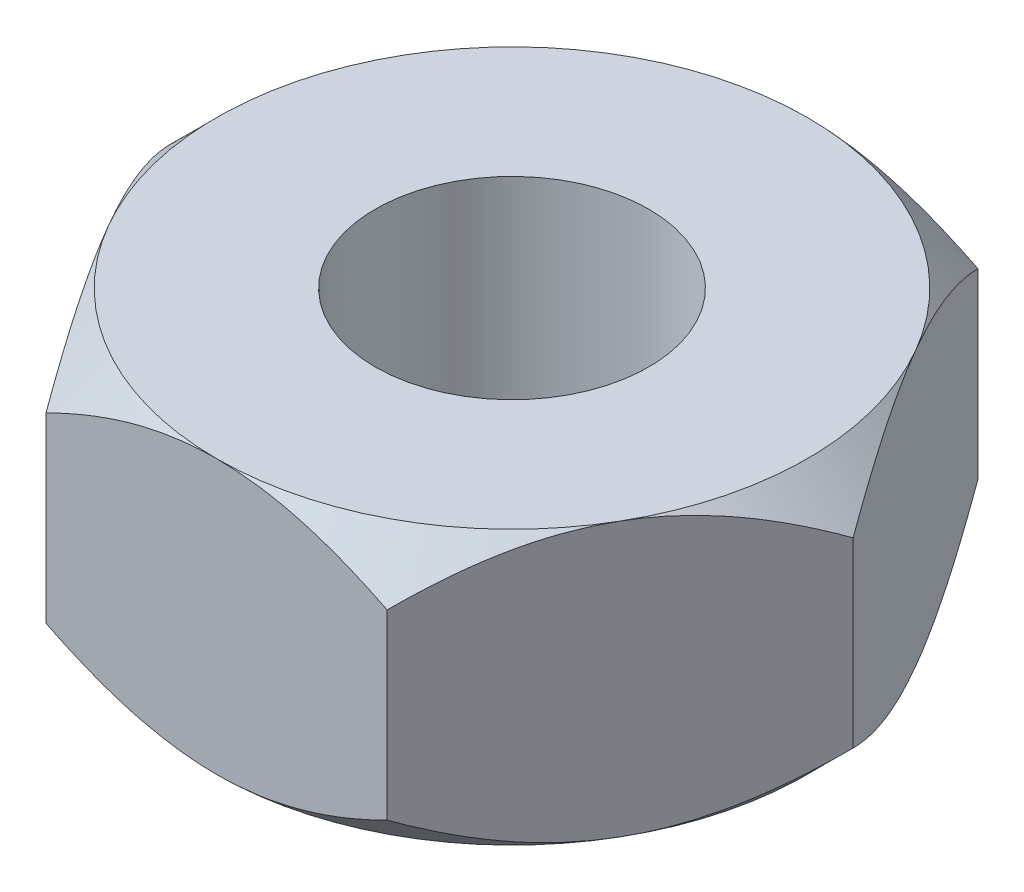
SolidWorks part; units mm, degrees
material "Nylon 6/10"
ref_plane "Front Plane" through (0, 0, 0) normal (0, 0, 1) x (1, 0, 0)
ref_plane "Top Plane" through (0, 0, 0) normal (0, 1, 0) x (1, 0, 0)
ref_plane "Right Plane" through (0, 0, 0) normal (1, 0, 0) x (0, 0, -1)
sketch "Sketch2" plane through (0, 0, 0) normal (0, 1, 0) x (1, 0, 0)
  line L1 (3.1177, 0) -> (1.5588, 2.7)
  line L2 (1.5588, 2.7) -> (-1.5588, 2.7)
  line L3 (-1.5588, 2.7) -> (-3.1177, 0)
  line L4 (-3.1177, 0) -> (-1.5588, -2.7)
  line L5 (-1.5588, -2.7) -> (1.5588, -2.7)
  line L6 (1.5588, -2.7) -> (3.1177, 0)
  circle A0 centre (0, 0) radius 2.7 construction
extrude "Boss-Extrude1" add sketch "Sketch2" along normal mid plane 2.5
hole_wizard "M3 Tapped Hole1" positions "3DSketch1" profile "Sketch3" tap size "M3" standard "ISO" end condition through all
sketch3d "3DSketch1"
  point P0 (0, 1.25, 0)
  point P3 (0, 0, 0)
  point P4 (0, 0, 0)
sketch "Sketch3" plane through (0, 1.25, 0) normal (1, 0, 0) x (0, 0, 1)
  line L0 (0, 0) -> (0, 2.5)
  line L1 (0, 2.5) -> (1.25, 2.5)
  line L2 (1.25, 2.5) -> (1.25, 0)
  line L5 (1.25, 0) -> (0, 0)
  line L11 (0, -6.35) -> (0, 107.95) construction
  dimension "Thru Tap Drill Dia." = 2.5
  dimension "Thru Tap Drill Depth" = 2.5
cosmetic thread "Hole Thread1" parameters "D2"=3
sketch "Sketch4" plane through (0, -1.25, 0) normal (0, -1, 0) x (1, 0, 0)
  line L0 (-3.1177, 0) -> (-1.5588, 2.7) construction
  circle A0 centre (0, 0) radius 2.7
extrude "Cut-Extrude1" cut sketch "Sketch4" along direction (0, -1, 0) on the side against the normal blind 2.5 draft 45 flip side to cut
mirror "Mirror1" about plane through (0, 0, 0) normal (0, 1, 0) of "Cut-Extrude1"
